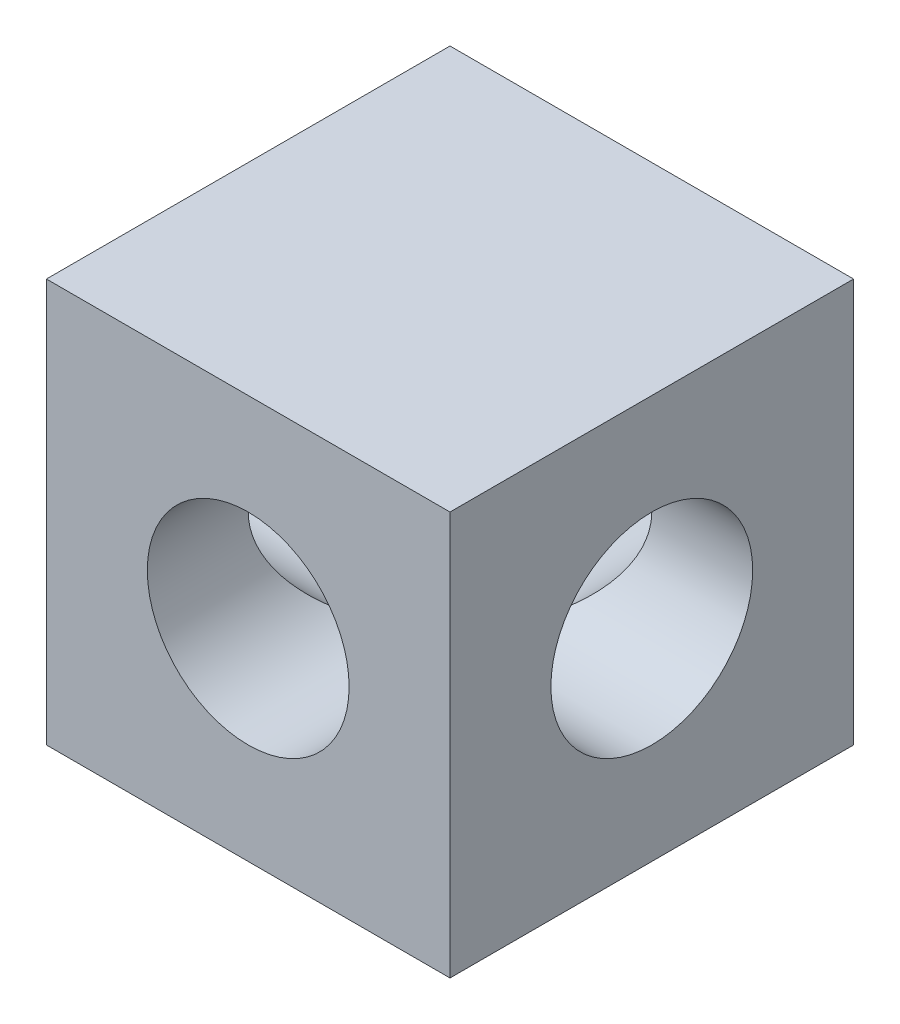
SolidWorks part; units mm, degrees
ref_plane "Front Plane" through (0, 0, 0) normal (0, 0, 1) x (1, 0, 0)
ref_plane "Top Plane" through (0, 0, 0) normal (0, 1, 0) x (1, 0, 0)
ref_plane "Right Plane" through (0, 0, 0) normal (1, 0, 0) x (0, 0, -1)
sketch "Sketch1" plane through (0, 0, 0) normal (0, 0, 1) x (1, 0, 0)
  line L1 (-10, -10) -> (10, -10)
  line L2 (-10, -10) -> (-10, 10)
  line L3 (-10, 10) -> (10, 10)
  line L4 (10, -10) -> (10, 10)
  line L5 (-10, -10) -> (10, 10) construction
  line L6 (-10, 10) -> (10, -10) construction
  point P0 (0, 0)
  dimension "D1" = 20
  dimension "D2" = 20
extrude "Boss-Extrude1" add sketch "Sketch1" along normal blind 20
sketch "Sketch2" plane through (0, 0, 20) normal (0, 0, 1) x (1, 0, 0)
  circle A0 centre (0, 0) radius 5
  dimension "D1" = 10
extrude "Cut-Extrude1" cut sketch "Sketch2" against normal blind 20
sketch "Sketch3" plane through (10, 0, 0) normal (1, 0, 0) x (0, 0, -1)
  line L0 (-10, 10) -> (-10, -10) construction
  line L1 (-20, 10) -> (0, 10) construction
  line L2 (-20, -10) -> (0, -10) construction
  circle A0 centre (-10, 0) radius 5
  dimension "D1" = 10
extrude "Cut-Extrude2" cut sketch "Sketch3" against normal blind 20
